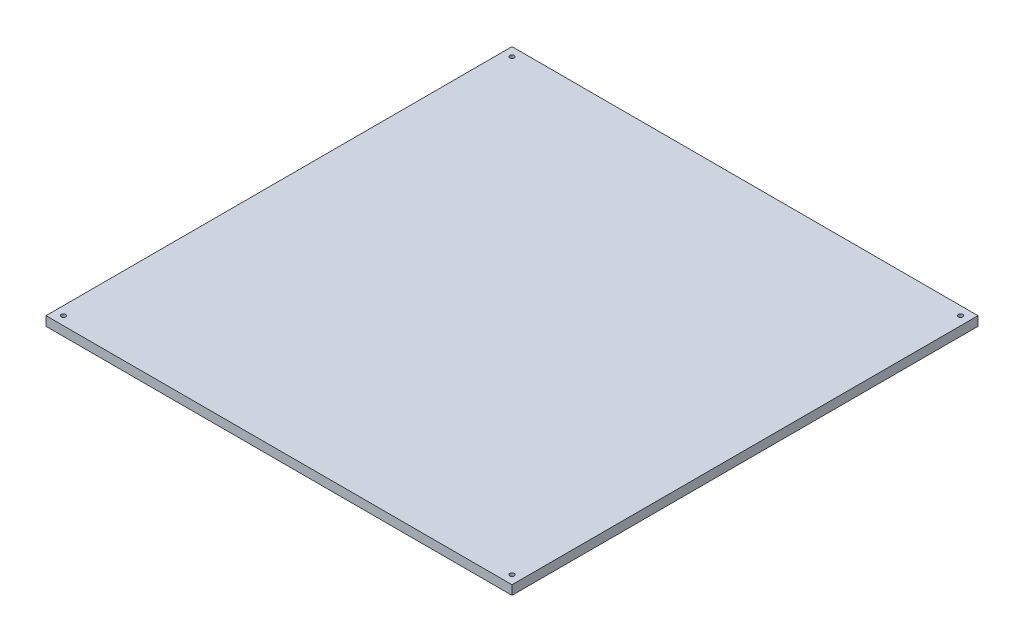
SolidWorks part; units mm, degrees
material "6061-T6 (SS)"
ref_plane "Front Plane" through (0, 0, 0) normal (0, 0, 1) x (1, 0, 0)
ref_plane "Top Plane" through (0, 0, 0) normal (0, 1, 0) x (1, 0, 0)
ref_plane "Right Plane" through (0, 0, 0) normal (1, 0, 0) x (0, 0, -1)
sketch "Sketch1" plane through (0, 0, 0) normal (0, 1, 0) x (1, 0, 0)
  line L0 (160, -160) -> (160, 160)
  line L1 (160, 160) -> (-160, 160)
  line L2 (-160, 160) -> (-160, -160)
  line L3 (-160, -160) -> (160, -160)
  line L4 (0, 160) -> (0, -160) construction
  line L5 (-160, 0) -> (160, 0) construction
  circle A0 centre (154, 154) radius 1.55
  circle A1 centre (-154, -154) radius 1.55
  circle A2 centre (154, -154) radius 1.55
  circle A3 centre (-154, 154) radius 1.55
  point P16 (-154, 155.55)
  point P17 (-155.55, 154)
  dimension "D2" = 308
  dimension "D3" = 308
  dimension "D4" = 3.1
  dimension "D1" = 320
extrude "Boss-Extrude1" add sketch "Sketch1" against normal blind 6.35
chamfer "Chamfer1" [suppressed] distance 3 angle 50
